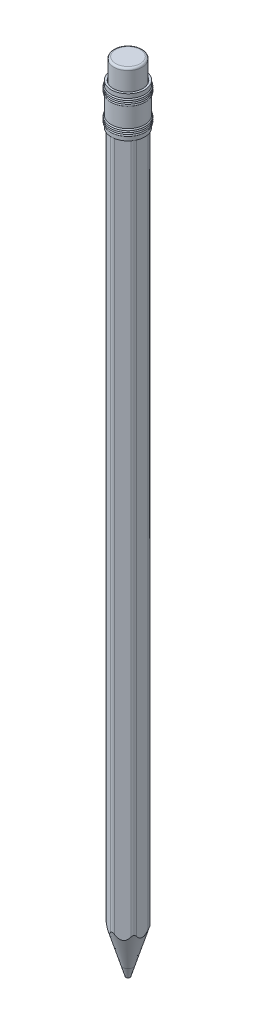
SolidWorks part; units mm, degrees
ref_plane "Front Plane" through (0, 0, 0) normal (0, 0, 1) x (1, 0, 0)
ref_plane "Top Plane" through (0, 0, 0) normal (0, 1, 0) x (1, 0, 0)
ref_plane "Right Plane" through (0, 0, 0) normal (1, 0, 0) x (0, 0, -1)
sketch "Sketch1" plane through (0, 0, 0) normal (0, 1, 0) x (1, 0, 0)
  circle A0 centre (0, 0) radius 1.25
  dimension "D1" = 2.5
extrude "lead" add sketch "Sketch1" along normal blind 185
sketch "Sketch2" plane through (0, 185, 0) normal (0, 1, 0) x (1, 0, 0)
  line L1 (3.5, 2.0207) -> (0, 4.0415)
  line L2 (0, 4.0415) -> (-3.5, 2.0207)
  line L3 (-3.5, 2.0207) -> (-3.5, -2.0207)
  line L4 (-3.5, -2.0207) -> (0, -4.0415)
  line L5 (0, -4.0415) -> (3.5, -2.0207)
  line L6 (3.5, -2.0207) -> (3.5, 2.0207)
  circle A0 centre (0, 0) radius 3.5 construction
  circle A1 centre (0, 0) radius 1.25
  circle A2 centre (0, 0) radius 1.25 construction
  dimension "D1" = 7
extrude "wooden casing" add sketch "Sketch2" against normal blind 185 separate body
sketch "Sketch7" plane through (0, 185, 0) normal (0, 1, 0) x (1, 0, 0)
  circle A0 centre (0, 0) radius 3.5
  dimension "D1" = 7
extrude "eraser" add sketch "Sketch7" along normal blind 10 separate body
fillet "Fillet1" radius 0.5 1 edges at (0, 195, 3.5)
sketch "Sketch8" plane through (0, 0, 0) normal (0, 0, 1) x (1, 0, 0)
  line L0 (0, 195) -> (0, 185) construction
  line L1 (3, 195) -> (-3, 195) construction
  line L2 (1.25, 185) -> (-1.25, 185) construction
  line L3 (0, 185) -> (-3.5, 185) construction
  line L4 (-4.1, 190) -> (-3.6, 190)
  line L5 (-4.1, 190) -> (-4.1, 180) construction
  line L6 (-4.1, 180) -> (-3.6, 180)
  line L7 (-3.6, 190) -> (-3.6, 180) construction
  line L8 (-4.1, 181.2) -> (-4.1, 181.6) construction
  line L9 (-4.1, 185) -> (-3.6, 185) construction
  line L10 (-4.1, 185) -> (-3.6, 185) construction
  line L11 (-4.1, 190) -> (-4.1, 189)
  line L12 (-4.1, 187.4) -> (-4.1, 182.6)
  line L13 (-4.1, 181) -> (-4.1, 180)
  line L14 (-3.85, 190) -> (-3.85, 180) construction
  line L15 (-3.6, 181.2) -> (-3.6, 181.6) construction
  line L16 (-3.6, 181) -> (-3.6, 180)
  line L17 (-3.6, 187.4) -> (-3.6, 182.6)
  line L18 (-3.6, 190) -> (-3.6, 189) construction
  line L19 (-3.6, 190) -> (-3.6, 189)
  arc A0 (-4.1, 181.4) -> (-4.1, 181) centre (-4.1, 181.2) ccw
  arc A1 (-4.1, 181.8) -> (-4.1, 181.4) centre (-4.1, 181.6) ccw
  arc A2 (-4.1, 182.2) -> (-4.1, 181.8) centre (-4.1, 182) ccw
  arc A3 (-4.1, 182.6) -> (-4.1, 182.2) centre (-4.1, 182.4) ccw
  arc A4 (-4.1, 188.6) -> (-4.1, 189) centre (-4.1, 188.8) cw
  arc A5 (-4.1, 188.2) -> (-4.1, 188.6) centre (-4.1, 188.4) cw
  arc A6 (-4.1, 187.8) -> (-4.1, 188.2) centre (-4.1, 188) cw
  arc A7 (-4.1, 187.4) -> (-4.1, 187.8) centre (-4.1, 187.6) cw
  arc A8 (-3.6, 187.4) -> (-3.6, 187.8) centre (-3.6, 187.6) ccw
  arc A9 (-3.6, 187.8) -> (-3.6, 188.2) centre (-3.6, 188) ccw
  arc A10 (-3.6, 188.2) -> (-3.6, 188.6) centre (-3.6, 188.4) ccw
  arc A11 (-3.6, 188.6) -> (-3.6, 189) centre (-3.6, 188.8) ccw
  arc A12 (-3.6, 182.6) -> (-3.6, 182.2) centre (-3.6, 182.4) cw
  arc A13 (-3.6, 182.2) -> (-3.6, 181.8) centre (-3.6, 182) cw
  arc A14 (-3.6, 181.8) -> (-3.6, 181.4) centre (-3.6, 181.6) cw
  arc A15 (-3.6, 181.4) -> (-3.6, 181) centre (-3.6, 181.2) cw
  dimension "D5" = 1
  dimension "D6" = 0.4
  dimension "D1" = 10
  dimension "D2" = 5
  dimension "D3" = 0.5
  dimension "D4" = 4.1
  dimension "D8" = 0.4
  dimension "D7" = 4
revolve "ferrule" add sketch "Sketch8" angle 360 about L0
fillet "Fillet2" radius 1 6 edges at (3.5, 92.5, -2.0207) (0, 92.5, -4.0415) (-3.5, 92.5, -2.0207) (3.5, 92.5, 2.0207) (-3.5, 92.5, 2.0207) (0, 92.5, 4.0415)
sketch "Sketch10" plane through (-1.75, 0, -3.0311) normal (-0.5, 0, -0.866) x (-0.866, 0, 0.5)
  line L0 (0.9434, 181.0472) -> (0.9434, 151.0472) construction
  line L5 (1.4434, 0) -> (1.4434, 185) construction
  text T0 "pencil 2b" font "Century Gothic" height in points 8
  dimension "D1" = 30
  dimension "D2" = 0.5
extrude "text" cut sketch "Sketch10" against normal blind 0.1
sketch "Sketch14" plane through (0, 0, 0) normal (0, 0, 1) x (1, 0, 0)
  line L0 (0, 0) -> (0, 16.59) construction
  line L1 (0.5, 0) -> (5, 0)
  line L2 (-1.25, 0) -> (1.25, 0) construction
  line L3 (5, 0) -> (5, 15)
  line L4 (5, 15) -> (0.5, 0)
  dimension "D1" = 15
  dimension "D2" = 0.5
  dimension "D3" = 5
revolve "Cut-Revolve1" cut sketch "Sketch14" angle 360 about L0
